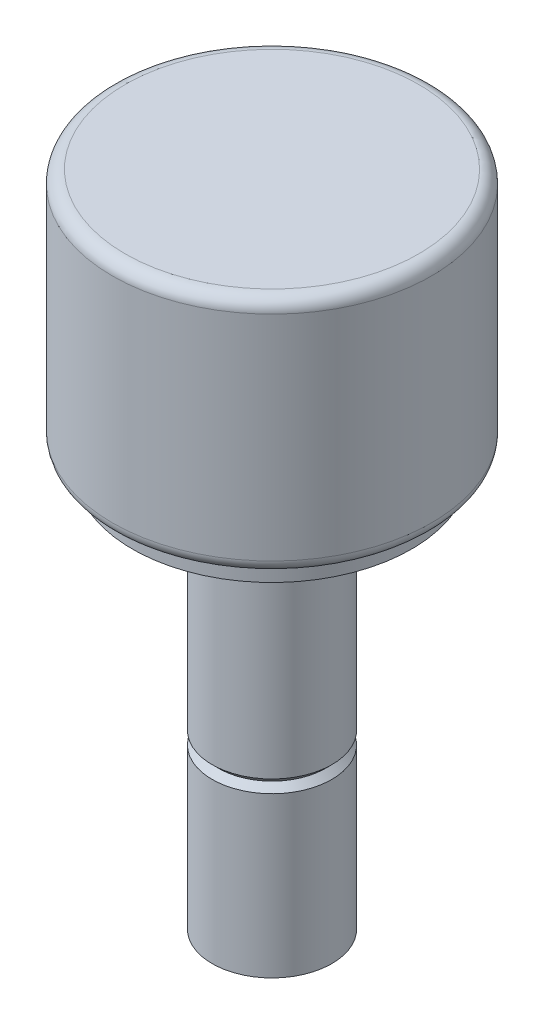
SolidWorks part; units mm, degrees
ref_plane "Front" through (0, 0, 0) normal (0, 0, 1) x (1, 0, 0)
ref_plane "Top" through (0, 0, 0) normal (0, 1, 0) x (1, 0, 0)
ref_plane "Right" through (0, 0, 0) normal (1, 0, 0) x (0, 0, -1)
sketch "Sketch1" plane through (0, 0, 0) normal (0, 0, 1) x (1, 0, 0)
  line L0 (0, 0) -> (0, 56.5416) construction
  line L1 (0, 0) -> (2.3813, 0)
  line L2 (2.3813, 0) -> (2.3813, 6.35)
  line L3 (2.3813, 6.35) -> (2.1272, 6.604)
  line L4 (2.1272, 6.604) -> (2.3813, 6.858)
  line L5 (2.3813, 6.858) -> (2.3813, 15.875)
  line L6 (2.3813, 15.875) -> (5.5563, 15.875)
  line L7 (5.5563, 15.875) -> (5.5563, 16.6687)
  line L8 (5.5563, 16.6687) -> (6.35, 16.6687)
  line L9 (6.35, 16.6687) -> (6.35, 26.1938)
  line L10 (6.35, 26.1938) -> (0, 26.1938)
  line L11 (0, 0) -> (0, 26.1938)
  dimension "D1" = 0.7937
  dimension "D2" = 9.525
  dimension "D3" = 12.7
  dimension "D4" = 4.7625
  dimension "D5" = 6.35
  dimension "D6" = 15.875
  dimension "D7" = 45
  dimension "D8" = 0.508
revolve "Revolve1" add sketch "Sketch1" angle 360 about L0
fillet "Fillet1" radius 0.508 2 edges at (0, 16.6687, -6.35) (0, 26.1938, -6.35)
